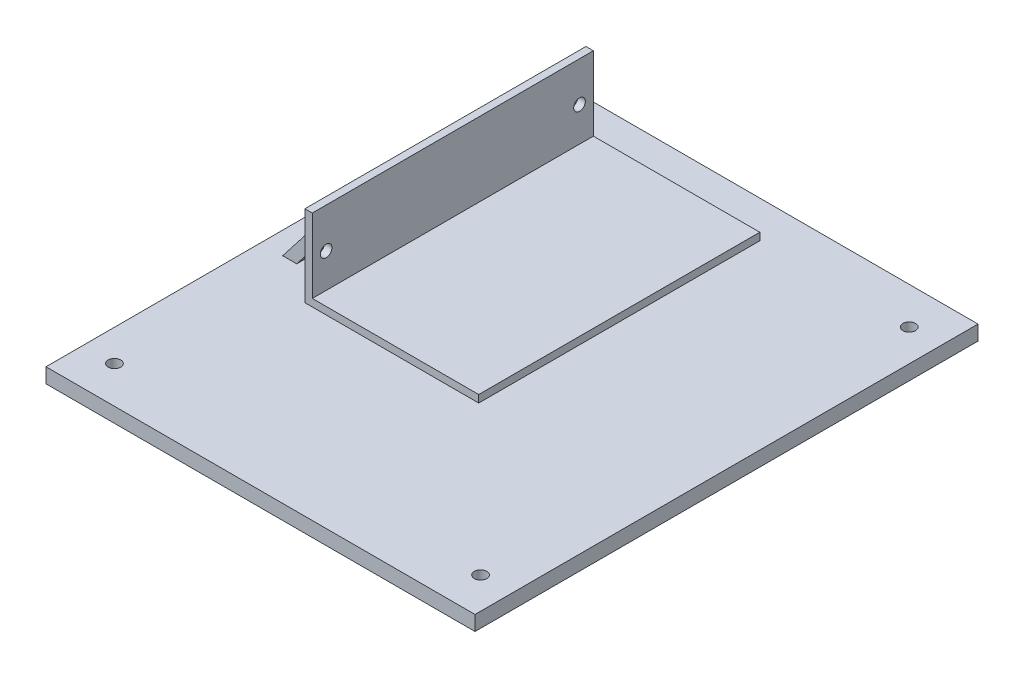
SolidWorks part; units mm, degrees
ref_plane "Front Plane" through (0, 0, 0) normal (0, 0, 1) x (1, 0, 0)
ref_plane "Top Plane" through (0, 0, 0) normal (0, 1, 0) x (1, 0, 0)
ref_plane "Right Plane" through (0, 0, 0) normal (1, 0, 0) x (0, 0, -1)
sketch "Sketch1" plane through (0, 0, 0) normal (0, 0, 1) x (1, 0, 0)
  line L1 (-73.66, -2.54) -> (73.66, -2.54)
  line L2 (-73.66, -2.54) -> (-73.66, 2.54)
  line L3 (-73.66, 2.54) -> (73.66, 2.54)
  line L4 (73.66, -2.54) -> (73.66, 2.54)
  line L5 (-73.66, -2.54) -> (73.66, 2.54) construction
  line L6 (-73.66, 2.54) -> (73.66, -2.54) construction
  point P0 (0, 0)
  dimension "D1" = 147.32
  dimension "D2" = 5.08
extrude "Boss-Extrude1" add sketch "Sketch1" along normal blind 172.72
sketch "Sketch2" plane through (0, 2.54, 0) normal (0, 1, 0) x (1, 0, 0)
  line L0 (73.66, -172.72) -> (-73.66, -172.72) construction
  line L1 (-73.66, -172.72) -> (-73.66, 0) construction
  line L2 (73.66, -172.72) -> (73.66, 0) construction
  line L3 (73.66, 0) -> (-73.66, 0) construction
  circle A0 centre (62.738, -12.7) radius 2.159
  circle A1 centre (-62.865, -160.02) radius 2.159
  circle A2 centre (62.865, -160.02) radius 2.159
  circle A3 centre (-62.738, -12.7) radius 2.159
  dimension "D1" = 4.318
  dimension "D7" = 4.318
  dimension "D2" = 10.922
  dimension "D3" = 12.7
  dimension "D4" = 12.7
  dimension "D5" = 10.795
  dimension "D6" = 10.795
  dimension "D8" = 12.7
  dimension "D9" = 10.922
  dimension "D10" = 12.7
extrude "Cut-Extrude1" cut sketch "Sketch2" against normal through all
sketch "Sketch3" plane through (0, 2.54, 0) normal (0, 1, 0) x (1, 0, 0)
  line L1 (-48.26, -12.7) -> (11.43, -12.7)
  line L2 (-48.26, -12.7) -> (-48.26, -109.22)
  line L3 (-48.26, -109.22) -> (11.43, -109.22)
  line L4 (11.43, -12.7) -> (11.43, -109.22)
  line L5 (73.66, 0) -> (-73.66, 0) construction
  line L6 (-73.66, -172.72) -> (-73.66, 0) construction
  dimension "D1" = 96.52
  dimension "D2" = 12.7
  dimension "D3" = 59.69
  dimension "D4" = 25.4
extrude "Boss-Extrude2" add sketch "Sketch3" along normal blind 2.54
sketch "Sketch4" plane through (0, 5.08, 0) normal (0, 1, 0) x (1, 0, 0)
  line L0 (-48.26, -109.22) -> (11.43, -109.22) construction
  line L1 (-48.26, -12.7) -> (-45.72, -12.7)
  line L2 (-48.26, -12.7) -> (-48.26, -109.22)
  line L3 (-48.26, -109.22) -> (-45.72, -109.22)
  line L4 (-45.72, -12.7) -> (-45.72, -109.22)
  dimension "D1" = 2.54
extrude "Boss-Extrude3" add sketch "Sketch4" along normal blind 25.4
sketch "Sketch5" plane through (-48.26, 0, 0) normal (-1, 0, 0) x (0, 0, 1)
  line L0 (12.7, 2.54) -> (109.22, 2.54) construction
  line L1 (22.86, 2.54) -> (99.06, 2.54)
  line L2 (22.86, 2.54) -> (22.86, 25.4)
  line L3 (22.86, 25.4) -> (99.06, 25.4)
  line L4 (99.06, 2.54) -> (99.06, 25.4)
  line L5 (12.7, 30.48) -> (12.7, 2.54) construction
  line L6 (109.22, 30.48) -> (109.22, 2.54) construction
  line L7 (12.7, 30.48) -> (109.22, 30.48) construction
  point P10 (109.22, 16.51)
  dimension "D1" = 10.16
  dimension "D2" = 10.16
  dimension "D3" = 5.08
extrude "Boss-Extrude4" add sketch "Sketch5" along normal blind 17.78
sketch "Sketch6" plane through (0, 0, 99.06) normal (0, 0, 1) x (1, 0, 0)
  line L0 (-66.04, 2.54) -> (-48.26, 25.4)
  line L1 (-66.04, 2.54) -> (-66.04, 25.4)
  line L2 (-66.04, 25.4) -> (-48.26, 25.4)
  line L3 (-61.2133, 2.54) -> (-48.26, 19.1942)
  line L4 (-66.04, 2.54) -> (-48.26, 2.54) construction
  line L5 (-48.26, 30.48) -> (-48.26, 2.54) construction
  line L6 (-48.26, 19.1942) -> (-48.26, 2.54)
  line L7 (-48.26, 2.54) -> (-61.2133, 2.54)
  dimension "D1" = 3.81
extrude "Cut-Extrude2" cut sketch "Sketch6" against normal through all
sketch "Sketch7" plane through (-45.72, 0, 0) normal (1, 0, 0) x (0, 0, -1)
  line L0 (-60.96, 5.08) -> (-60.96, 16.83) construction
  line L1 (-109.22, 5.08) -> (-12.7, 5.08) construction
  line L2 (-104.46, 16.83) -> (-17.46, 16.83) construction
  circle A0 centre (-104.46, 16.83) radius 2
  circle A1 centre (-17.46, 16.83) radius 2
  point P7 (-60.96, 16.83)
  dimension "D3" = 4
  dimension "D1" = 11.75
  dimension "D2" = 87
extrude "Cut-Extrude3" cut sketch "Sketch7" against normal through all
